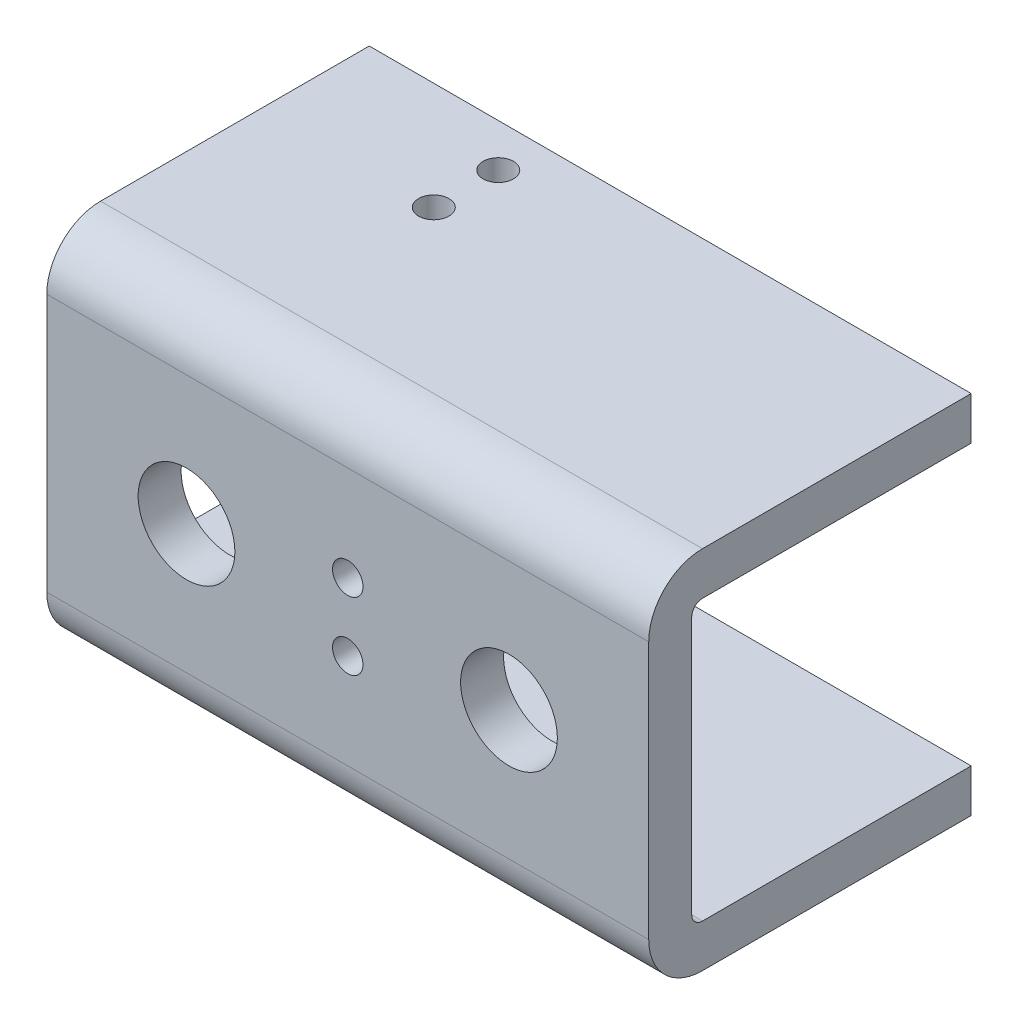
SolidWorks part; units mm, degrees
ref_plane "Front Plane" through (0, 0, 0) normal (0, 0, 1) x (1, 0, 0)
ref_plane "Top Plane" through (0, 0, 0) normal (0, 1, 0) x (1, 0, 0)
ref_plane "Right Plane" through (0, 0, 0) normal (1, 0, 0) x (0, 0, -1)
sketch "Sketch1" plane through (0, 0, 0) normal (0, 0, 1) x (1, 0, 0)
  line L0 (-44.45, 0) -> (44.45, 0) construction
  line L1 (-44.45, 26.9875) -> (44.45, 26.9875)
  line L2 (-44.45, 26.9875) -> (-44.45, -26.9875)
  line L3 (-44.45, -26.9875) -> (44.45, -26.9875)
  line L4 (44.45, 26.9875) -> (44.45, -26.9875)
  line L5 (0, 20.6375) -> (0, -20.6375) construction
  dimension "D1" = 53.975
  dimension "A" = 88.9
  dimension "B" = 41.275
extrude "Boss-Extrude1" add sketch "Sketch1" along normal mid plane 41.275
fillet "Fillet1" radius 7.9375 2 edges at (0, -26.9875, 20.6375) (0, 26.9875, 20.6375)
sketch "Sketch3" plane through (0, 0, -20.6375) normal (0, 0, -1) x (-1, 0, 0)
  line L4 (44.45, -26.9875) -> (44.45, 26.9875)
  line L5 (44.45, 26.9875) -> (-44.45, 26.9875)
  line L6 (-44.45, 26.9875) -> (-44.45, -26.9875)
  line L7 (-44.45, -26.9875) -> (44.45, -26.9875)
  line L8 (44.45, -26.9875) -> (44.45, 26.9875)
  line L9 (44.45, 26.9875) -> (-44.45, 26.9875)
  line L10 (-44.45, 26.9875) -> (-44.45, -26.9875)
  line L11 (-44.45, -26.9875) -> (44.45, -26.9875)
  dimension "D1" = 0
extrude "Boss-Extrude2" add sketch "Sketch3" along normal blind 6.35
shell "Shell1" thickness 6.35
sketch "Sketch2" plane through (0, 0, 20.6375) normal (0, 0, 1) x (1, 0, 0)
  line L0 (-23.8125, 0) -> (23.8125, 0) construction
  circle A0 centre (-23.8125, 0) radius 7.1438
  circle A1 centre (23.8125, 0) radius 7.1438
  dimension "Hole Size" = 14.2875
  dimension "Spacing" = 47.625
extrude "Cut-Extrude1" cut sketch "Sketch2" against normal blind 47.625
hole_wizard "#16 (0.177) Diameter Hole1" positions "Sketch6" profile "Sketch7" hole size "#16" standard "ANSI Inch" end condition through all
sketch "Sketch6" plane through (0, 26.9875, 0) normal (0, 1, 0) x (1, 0, 0)
  line L0 (-19.05, 11.1125) -> (-19.05, 20.6375) construction
  line L2 (-44.45, -12.7) -> (-44.45, 26.9875) construction
  line L3 (-44.45, 26.9875) -> (44.45, 26.9875) construction
  point P0 (-19.05, 11.1125)
  point P2 (-19.05, 20.6375)
  dimension "D1" = 9.525
  dimension "D2" = 25.4
  dimension "D3" = 6.35
sketch "Sketch7" plane through (-19.05, 26.9875, -11.1125) normal (1, 0, 0) x (0, 0, 1)
  line L0 (0, 0) -> (0, 53.975)
  line L1 (0, 53.975) -> (2.2479, 53.975)
  line L2 (2.2479, 53.975) -> (2.2479, 0)
  line L5 (2.2479, 0) -> (0, 0)
  line L11 (0, -6.35) -> (0, 107.95) construction
  dimension "Thru Hole Dia." = 4.4958
  dimension "Thru Hole Depth" = 53.975
hole_wizard "#16 (0.177) Diameter Hole2" positions "Sketch8" profile "Sketch9" hole size "#16" standard "ANSI Inch" end condition through all
sketch "Sketch8" plane through (0, 0, 20.6375) normal (0, 0, 1) x (1, 0, 0)
  line L0 (0, 0) -> (0, 5) construction
  line L2 (0, 0) -> (0, -5) construction
  point P0 (0, -5)
  point P2 (0, 5)
  point P12 (0, 4.3271)
  dimension "D1" = 10
sketch "Sketch9" plane through (0, -5, 20.6375) normal (1, 0, 0) x (0, -1, 0)
  line L0 (0, 0) -> (0, 47.625)
  line L1 (0, 47.625) -> (2.2479, 47.625)
  line L2 (2.2479, 47.625) -> (2.2479, 0)
  line L5 (2.2479, 0) -> (0, 0)
  line L11 (0, -6.35) -> (0, 107.95) construction
  dimension "Thru Hole Dia." = 4.4958
  dimension "Thru Hole Depth" = 47.625
equation "\"D1@Sketch1\" = (\"Thickness@Shell1\"*2)+1.625"
